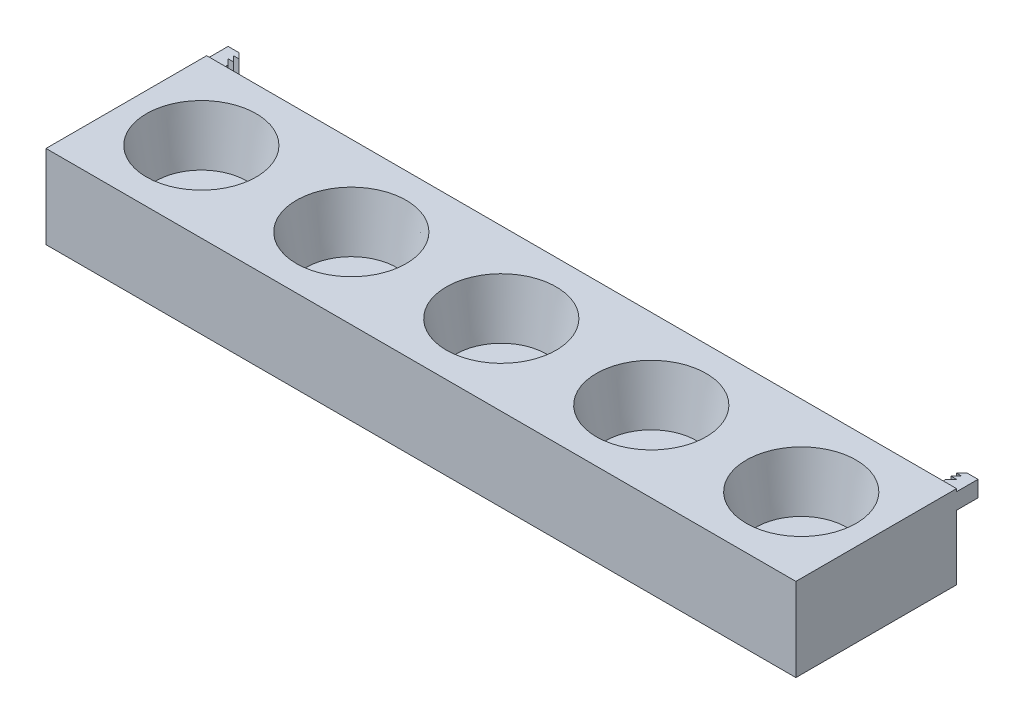
SolidWorks part; units mm, degrees
ref_plane "Front Plane" through (0, 0, 0) normal (0, 0, 1) x (1, 0, 0)
ref_plane "Top Plane" through (0, 0, 0) normal (0, 1, 0) x (1, 0, 0)
ref_plane "Right Plane" through (0, 0, 0) normal (1, 0, 0) x (0, 0, -1)
sketch "Sketch1" plane through (0, 0, 0) normal (0, 1, 0) x (1, 0, 0)
  line L1 (350, 75) -> (-350, 75)
  line L2 (350, 75) -> (350, -75)
  line L3 (350, -75) -> (-350, -75)
  line L4 (-350, 75) -> (-350, -75)
  line L5 (350, 75) -> (-350, -75) construction
  line L6 (350, -75) -> (-350, 75) construction
  point P0 (0, 0)
extrude "Boss-Extrude1" add sketch "Sketch1" along normal blind 20 and the other way blind 57.8
sketch "Sketch3" plane through (0, 0, -75) normal (0, 0, -1) x (-1, 0, 0)
  line L0 (-350, 20) -> (-350, -57.8) construction
  line L1 (-335, 17.5) -> (-350, 17.5)
  line L2 (-335, 17.5) -> (-335, 2.5)
  line L3 (-335, 2.5) -> (-350, 2.5)
  line L4 (-350, 17.5) -> (-350, 2.5)
  line L5 (-335, 17.5) -> (-350, 2.5) construction
  line L6 (-335, 2.5) -> (-350, 17.5) construction
  line L7 (335, 17.5) -> (335, 2.5)
  line L8 (350, 17.5) -> (350, 2.5)
  line L9 (350, 17.5) -> (335, 17.5)
  line L10 (350, 2.5) -> (335, 2.5)
  point P0 (-342.5, 10)
  dimension "D1" = 2
extrude "Boss-Extrude2" add sketch "Sketch3" along normal blind 20
sketch "Sketch4" plane through (0, 17.5, 0) normal (0, 1, 0) x (1, 0, 0)
  line L0 (335, 95) -> (340, 95)
  line L1 (335, 95) -> (350, 95) construction
  line L2 (335, 95) -> (335, 90)
  line L3 (335, 95) -> (335, 75) construction
  line L4 (340, 95) -> (335, 90)
  line L5 (340, 90) -> (335, 85)
  line L6 (335, 90) -> (340, 90)
  line L7 (335, 90) -> (335, 85)
  line L8 (340, 85) -> (335, 80)
  line L9 (335, 85) -> (340, 85)
  line L10 (335, 85) -> (335, 80)
  line M6 (335, 95) -> (335, 75)
  dimension "D1" = 3
extrude "Cut-Extrude1" cut sketch "Sketch4" against normal blind 15 contours L6 L5 M6 | L9 L8 M6 | L2 L4 L0
sketch "Sketch5" plane through (0, 17.5, 0) normal (0, 1, 0) x (1, 0, 0)
  line L0 (-335, 95) -> (-335, 90)
  line L1 (-335, 95) -> (-335, 75) construction
  line L2 (-335, 95) -> (-340, 95)
  line L3 (-350, 95) -> (-335, 95) construction
  line L4 (-340, 95) -> (-335, 90)
  line L5 (-340, 90) -> (-335, 85)
  line L6 (-335, 90) -> (-335, 85)
  line L7 (-335, 90) -> (-340, 90)
  line L8 (-340, 85) -> (-335, 80)
  line L9 (-335, 85) -> (-335, 80)
  line L10 (-335, 85) -> (-340, 85)
  line M4 (-335, 75) -> (-335, 95)
  line M5 (-335, 95) -> (-350, 95)
  dimension "D1" = 3
extrude "Cut-Extrude2" cut sketch "Sketch5" against normal blind 15 contours L7 L5 M4 | L4 M5 M4 | L10 L8 M4
sketch "Sketch6" plane through (0, 20, 0) normal (0, 1, 0) x (1, 0, 0)
  circle A0 centre (0, 0) radius 51.25
  circle A1 centre (140, 0) radius 51.25
  circle A2 centre (280, 0) radius 51.25
  circle A3 centre (-140, 0) radius 51.25
  circle A4 centre (-280, 0) radius 51.25
  dimension "D1" = 3
  dimension "D2" = 3
extrude "Cut-Extrude3" cut sketch "Sketch6" against normal blind 50 draft 10 contours A0
sketch "Sketch7" plane through (0, 20, 0) normal (0, 1, 0) x (1, 0, 0)
  circle A0 centre (140, 0) radius 51.25
extrude "Cut-Extrude4" cut sketch "Sketch7" against normal blind 50 draft 10
sketch "Sketch8" plane through (0, 20, 0) normal (0, 1, 0) x (1, 0, 0)
  circle A0 centre (280, 0) radius 51.25
extrude "Cut-Extrude5" cut sketch "Sketch8" against normal blind 50 draft 10
sketch "Sketch9" plane through (0, 20, 0) normal (0, 1, 0) x (1, 0, 0)
  circle A0 centre (-140, 0) radius 51.25
extrude "Cut-Extrude6" cut sketch "Sketch9" against normal blind 50 draft 10
sketch "Sketch10" plane through (0, 20, 0) normal (0, 1, 0) x (1, 0, 0)
  circle A0 centre (-280, 0) radius 51.25
extrude "Cut-Extrude7" cut sketch "Sketch10" against normal blind 50 draft 10
